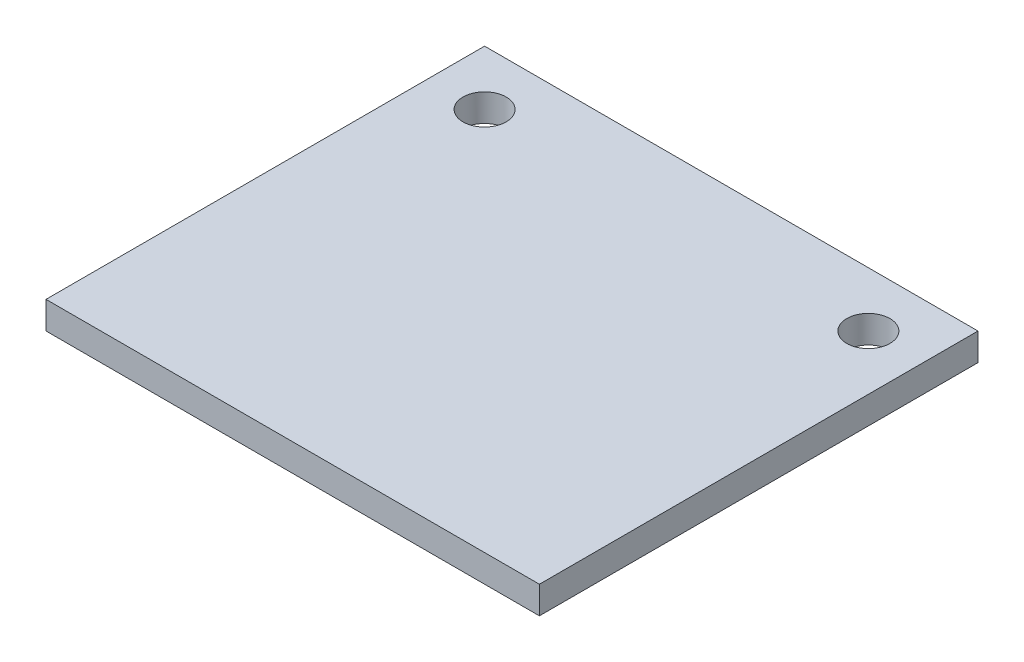
SolidWorks part; units mm, degrees
ref_plane "Front Plane" through (0, 0, 0) normal (0, 0, 1) x (1, 0, 0)
ref_plane "Top Plane" through (0, 0, 0) normal (0, 1, 0) x (1, 0, 0)
ref_plane "Right Plane" through (0, 0, 0) normal (1, 0, 0) x (0, 0, -1)
sketch "Sketch1" plane through (0, 0, 0) normal (0, 1, 0) x (1, 0, 0)
  line L1 (-11.43, -10.16) -> (11.43, -10.16)
  line L2 (-11.43, -10.16) -> (-11.43, 10.16)
  line L3 (-11.43, 10.16) -> (11.43, 10.16)
  line L4 (11.43, -10.16) -> (11.43, 10.16)
  line L5 (-11.43, -10.16) -> (11.43, 10.16) construction
  line L6 (-11.43, 10.16) -> (11.43, -10.16) construction
  point P0 (0, 0)
  dimension "D1" = 22.86
  dimension "D2" = 20.32
extrude "Boss-Extrude1" add sketch "Sketch1" along normal mid plane 1.27
sketch "Sketch2" plane through (0, 0.635, 0) normal (0, 1, 0) x (1, 0, 0)
  line L0 (11.43, 10.16) -> (-11.43, 10.16) construction
  line L1 (-11.43, 10.16) -> (-11.43, -10.16) construction
  line L2 (0, -55) -> (0, 55) construction
  circle A0 centre (-8.89, 7.62) radius 1
  circle A1 centre (8.89, 7.62) radius 1
  dimension "D1" = 2
  dimension "D2" = 2.54
  dimension "D3" = 2.54
extrude "Cut-Extrude1" cut sketch "Sketch2" against normal through all both and the other way through all
